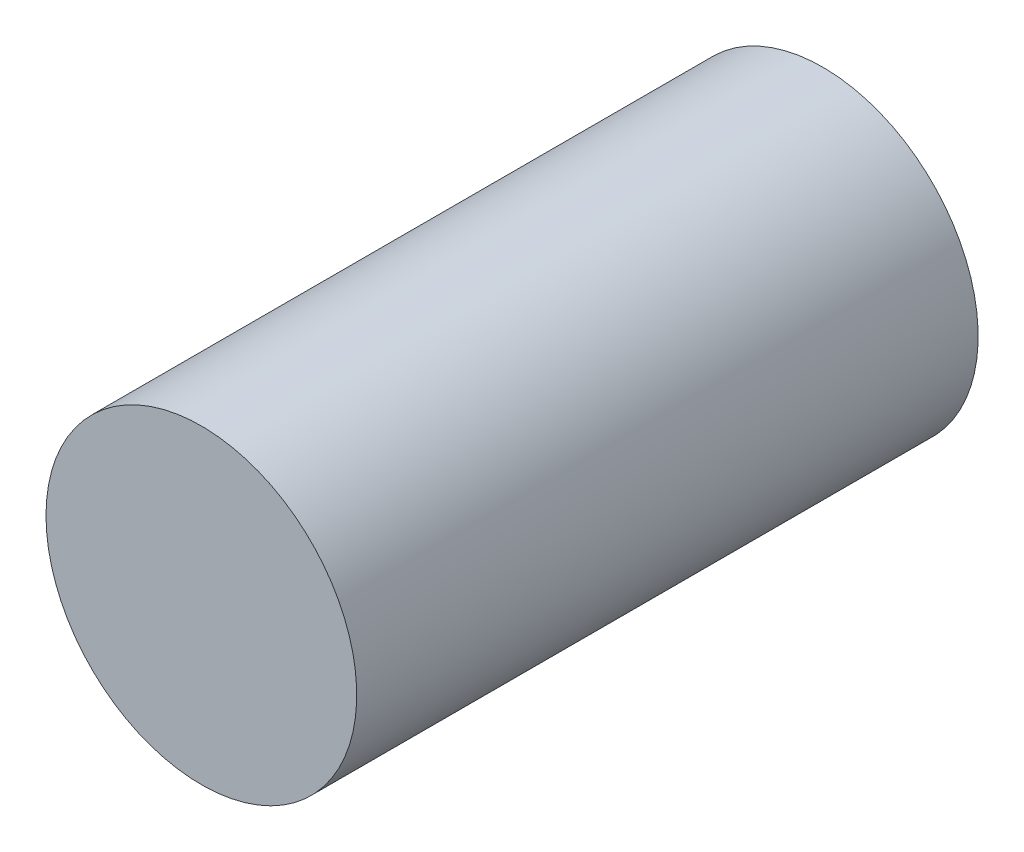
SolidWorks part; units mm, degrees
ref_plane "Front Plane" through (0, 0, 0) normal (0, 0, 1) x (1, 0, 0)
ref_plane "Top Plane" through (0, 0, 0) normal (0, 1, 0) x (1, 0, 0)
ref_plane "Right Plane" through (0, 0, 0) normal (1, 0, 0) x (0, 0, -1)
sketch "Sketch1" plane through (0, 0, 0) normal (0, 1, 0) x (1, 0, 0)
  line L0 (0, 1165.3407) -> (0, -53.8593)
  line L1 (0, 1165.3407) -> (304.8, 1165.3407)
  line L2 (0, -53.8593) -> (304.8, -53.8593)
  line L3 (304.8, 1165.3407) -> (304.8, -53.8593)
  point P4 (0, 0)
revolve "Revolve1" add sketch "Sketch1" angle 360 about L0
sketch "Sketch2" plane through (0, 0, 53.8593) normal (0, 0, 1) x (1, 0, 0)
  line L0 (304.8, 0) -> (-304.8, 0)
  circle A0 centre (0, 0) radius 304.8 construction
sketch "Sketch3" plane through (0, 0, -1165.3407) normal (0, 0, -1) x (-1, 0, 0)
  line L0 (0, 0) -> (-304.8, 0)
  line L1 (0, 0) -> (304.8, 0)
  circle A0 centre (0, 0) radius 304.8 construction
sketch3d "3DSketch2"
  line L0 (-304.8, 0, -1165.3407) -> (-304.7927, -2.1147, 53.8593)
  line L1 (304.8, 0, -1165.3407) -> (304.8, 0, 53.8593)
  circle A0 centre (0, 0, 53.8593) radius 304.8 construction
  point P5 (0, 0, -250.9407)
